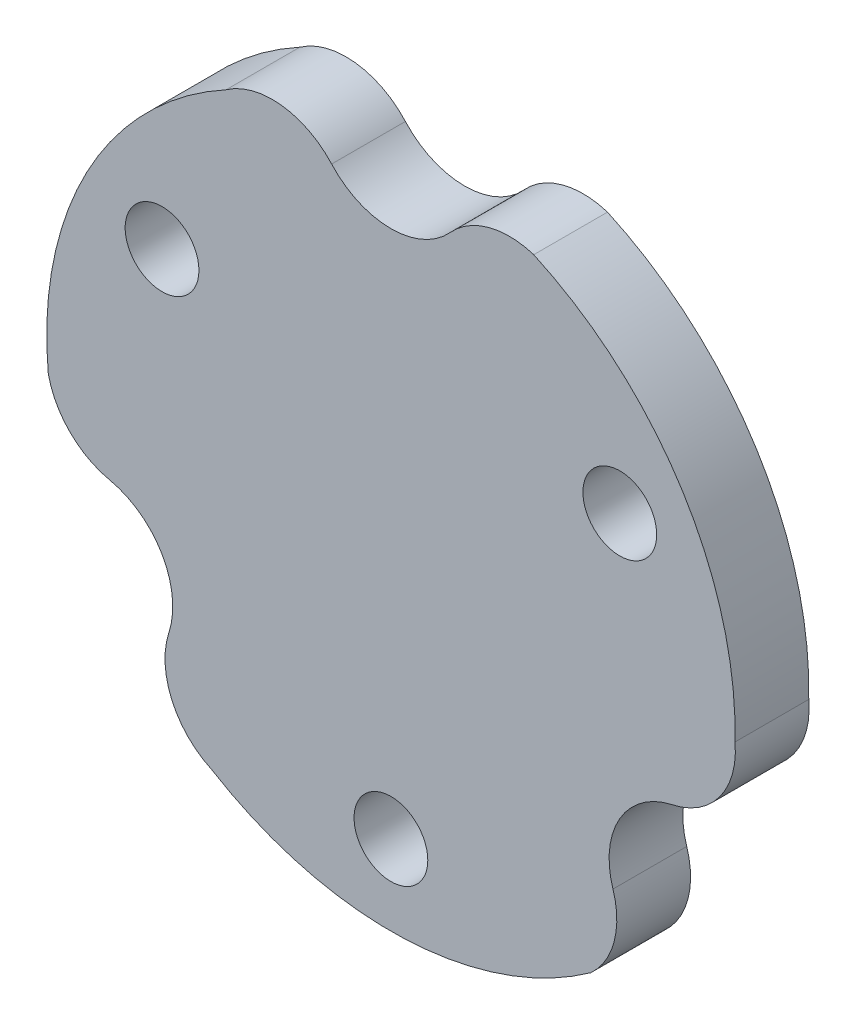
SolidWorks part; units mm, degrees
ref_plane "Plan de face" through (0, 0, 0) normal (0, 0, 1) x (1, 0, 0)
ref_plane "Plan de dessus" through (0, 0, 0) normal (0, 1, 0) x (1, 0, 0)
ref_plane "Plan de droite" through (0, 0, 0) normal (1, 0, 0) x (0, 0, -1)
sketch "Esquisse1" plane through (0, 0, 0) normal (0, 0, 1) x (1, 0, 0)
  line L0 (9.3098, 5.375) -> (0, -10.75) construction
  line L1 (0, -10.75) -> (-9.3098, 5.375) construction
  line L2 (-9.3098, 5.375) -> (9.3098, 5.375) construction
  arc A12 (-2.411, 11.8207) -> (2.411, 11.8207) centre (0, 14) ccw
  arc A16 (5.8094, 12.7378) -> (2.411, 11.8207) centre (4.8221, 9.6414) ccw
  arc A17 (-2.411, 11.8207) -> (-6.7074, 12.2887) centre (-4.8221, 9.6414) ccw
  arc A18 (-6.7074, 12.2887) -> (-13.9359, -1.3378) centre (0, 0) ccw
  arc A19 (8.1265, -11.4) -> (9.0315, -7.9984) centre (5.9386, -8.9967) ccw
  arc A20 (11.4425, -3.8223) -> (9.0315, -7.9984) centre (12.1244, -7) ccw
  arc A21 (11.4425, -3.8223) -> (13.996, -0.3356) centre (10.7607, -0.6447) ccw
  arc A23 (-13.9359, -1.3378) -> (-11.4425, -3.8223) centre (-10.7607, -0.6447) ccw
  arc A24 (-9.0315, -7.9984) -> (-11.4425, -3.8223) centre (-12.1244, -7) ccw
  arc A25 (-9.0315, -7.9984) -> (-7.2886, -11.9531) centre (-5.9386, -8.9967) ccw
  arc A27 (-7.2886, -11.9531) -> (8.1265, -11.4) centre (0, 0) ccw
  arc A28 (13.996, -0.3356) -> (5.8094, 12.7378) centre (0, 0) ccw
  circle A30 centre (0, 0) radius 10.75 construction
  circle A31 centre (9.3098, 5.375) radius 1.5
  circle A32 centre (0, -10.75) radius 1.5
  circle A33 centre (-9.3098, 5.375) radius 1.5
  circle A34 centre (9.3098, 5.375) radius 3.25 construction
  circle A35 centre (-9.3098, 5.375) radius 3.25 construction
  circle A36 centre (0, -10.75) radius 3.25 construction
  point P31 (0, 0)
  dimension "D2" = 3
  dimension "D3" = 6.5
  dimension "D4" = 6.5
  dimension "D8" = 14
  dimension "D9" = 3.25
  dimension "D10" = 6.5
  dimension "D11" = 3.25
  dimension "D6" = 60
  dimension "D7" = 60
  dimension "D14" = 10.78
  dimension "D15" = 10.78
extrude "Boss.-Extru.2" add sketch "Esquisse1" along normal blind 3
